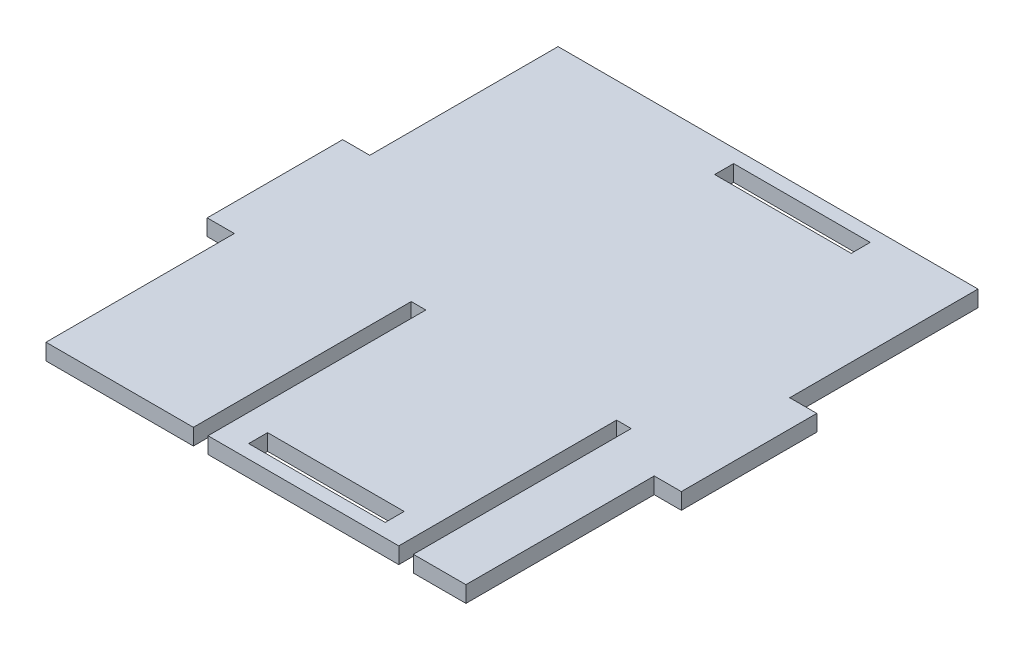
SolidWorks part; units mm, degrees
ref_plane "Front Plane" through (0, 0, 0) normal (0, 0, 1) x (1, 0, 0)
ref_plane "Top Plane" through (0, 0, 0) normal (0, 1, 0) x (1, 0, 0)
ref_plane "Right Plane" through (0, 0, 0) normal (1, 0, 0) x (0, 0, -1)
sketch "Sketch1" plane through (0, 0, 0) normal (0, 1, 0) x (1, 0, 0)
  line L0 (-85.2, 5) -> (-34.8, 5)
  line L1 (0, 0) -> (-155, 0)
  line L2 (0, 0) -> (0, 189)
  line L3 (0, 189) -> (-155, 189)
  line L4 (-155, 0) -> (-155, 189)
  line L6 (0, 94.5) -> (-155, 94.5) construction
  line L7 (-100.6, 0) -> (-95.2, 0)
  line L8 (-100.6, 0) -> (-100.6, 80.4)
  line L9 (-100.6, 80.4) -> (-95.2, 80.4)
  line L10 (-95.2, 0) -> (-95.2, 80.4)
  line L11 (-97.9, 80.4) -> (-97.9, 0) construction
  line L12 (-100.6, 40.2) -> (-95.2, 40.2) construction
  line L13 (-24.8, 0) -> (-19.4, 0)
  line L14 (-24.8, 0) -> (-24.8, 80.4)
  line L15 (-24.8, 80.4) -> (-19.4, 80.4)
  line L16 (-19.4, 0) -> (-19.4, 80.4)
  line L17 (-22.1, 80.4) -> (-22.1, 0) construction
  line L18 (-24.8, 40.2) -> (-19.4, 40.2) construction
  line L19 (0, 69.5) -> (10, 69.5)
  line L21 (0, 119.5) -> (10, 119.5)
  line L22 (10, 69.5) -> (10, 119.5)
  line L23 (0, 94.5) -> (10, 94.5) construction
  line L24 (0, 119.5) -> (0, 69.5)
  line L25 (-75, 0) -> (-25, 0)
  line L26 (-85.2, 5) -> (-85.2, 12)
  line L27 (-85.2, 12) -> (-34.8, 12)
  line L28 (-34.8, 5) -> (-34.8, 12)
  line L30 (-85.2, 5) -> (-35.2, 5) construction
  line L31 (-85.2, 184) -> (-34.8, 184)
  line L32 (-34.8, 184) -> (-34.8, 177)
  line L33 (-85.2, 177) -> (-34.8, 177)
  line L34 (-85.2, 184) -> (-85.2, 177)
  line L35 (-155, 119.5) -> (-165, 119.5)
  line L36 (-165, 69.5) -> (-165, 119.5)
  line L37 (-155, 69.5) -> (-165, 69.5)
  line L38 (-155, 119.5) -> (-155, 69.5)
  point P92 (-97.9, 40.2)
  point P133 (-22.1, 40.2)
  point P212 (-50, 94.5)
  point P216 (-60, 5)
  dimension "D2" = 10
  dimension "D3" = 5
  dimension "D4" = 7
  dimension "D5" = 19.4
  dimension "D6" = 189
  dimension "D7" = 50
  dimension "D8" = 50.4
  dimension "D9" = 80.4
  dimension "D10" = 5.4
  dimension "D11" = 5.4
  dimension "D12" = 10
  dimension "D13" = 10
  dimension "D14" = 155
extrude "Boss-Extrude1" add sketch "Sketch1" along normal blind 6 contours L16 L1 L2 L3 L4 L8 L9 L10 L14 L15 L34 L31 L32 L33 L28 L0 L26 L27 | L37 L4 L35 L36 | L19 L22 L21 L2
